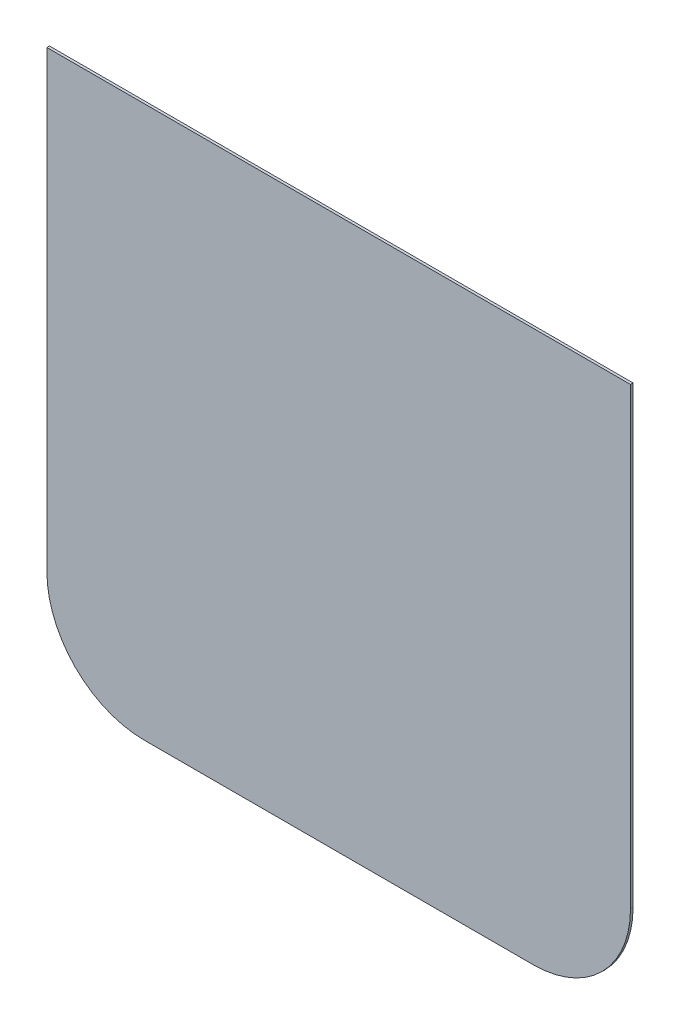
SolidWorks part; units mm, degrees
ref_plane "Спереди" through (0, 0, 0) normal (0, 0, 1) x (1, 0, 0)
ref_plane "Сверху" through (0, 0, 0) normal (0, 1, 0) x (1, 0, 0)
ref_plane "Справа" through (0, 0, 0) normal (1, 0, 0) x (0, 0, -1)
sketch "Эскиз1" plane through (0, 0, 0) normal (0, 0, 1) x (1, 0, 0)
  line L0 (-260.936, 123.1156) -> (-260.936, -226.8844)
  line L5 (-185.936, -301.8844) -> (114.064, -301.8844)
  line L6 (189.064, 123.1156) -> (189.064, -226.8844)
  line L7 (-260.936, 123.1156) -> (164.064, 123.1156)
  line L8 (164.064, 123.1156) -> (189.064, 123.1156)
  arc A2 (-260.936, -226.8844) -> (-185.936, -301.8844) centre (-185.936, -226.8844) ccw
  arc A3 (114.064, -301.8844) -> (189.064, -226.8844) centre (114.064, -226.8844) ccw
extrude "Бобышка-Вытянуть2" add sketch "Эскиз1" along normal blind 2
